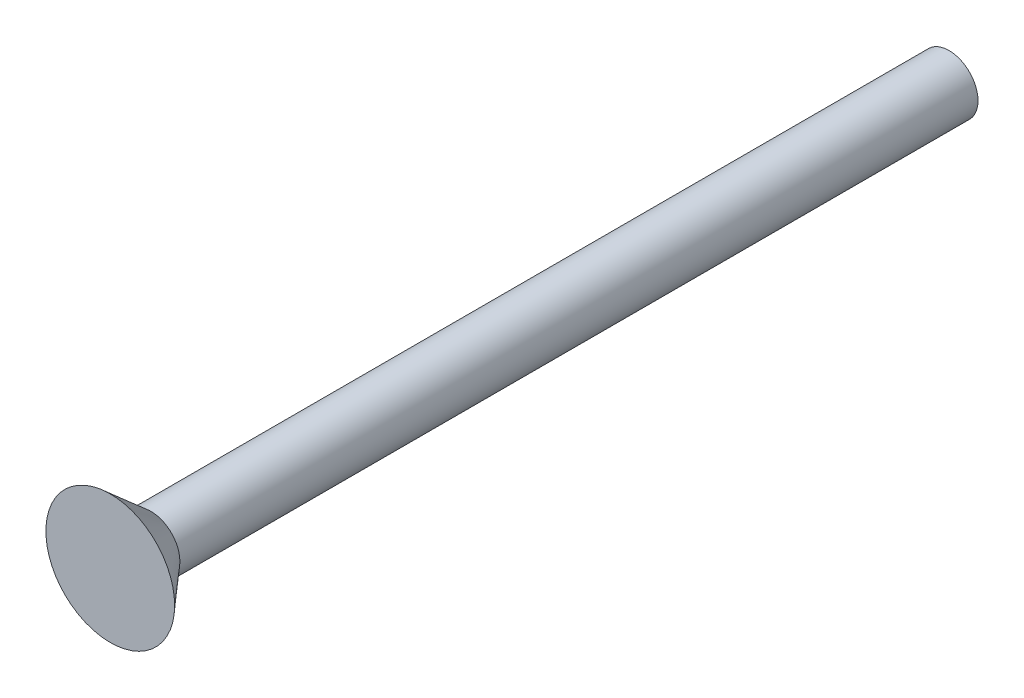
SolidWorks part; units mm, degrees
ref_plane "Front Plane" through (0, 0, 0) normal (0, 0, 1) x (1, 0, 0)
ref_plane "Top Plane" through (0, 0, 0) normal (0, 1, 0) x (1, 0, 0)
ref_plane "Right Plane" through (0, 0, 0) normal (1, 0, 0) x (0, 0, -1)
sketch "Sketch1" plane through (0, 0, 0) normal (0, 0, 1) x (1, 0, 0)
  circle A0 centre (0, 0) radius 1.7526
extrude "Boss-Extrude1" add sketch "Sketch1" against normal blind 50.8
sketch "Sketch3" plane through (0, 0, 0) normal (1, 0, 0) x (0, 0, -1)
  line L0 (0, 0) -> (2.4638, 0)
  line L1 (2.4638, 0) -> (2.4638, 1.7526)
  line L2 (50.8, 1.7526) -> (0, 1.7526) construction
  line L3 (0, 0) -> (0, 3.8989)
  line L4 (0, 3.8989) -> (2.4638, 1.7526)
revolve "Revolve1" add sketch "Sketch3" angle 360 about L0
